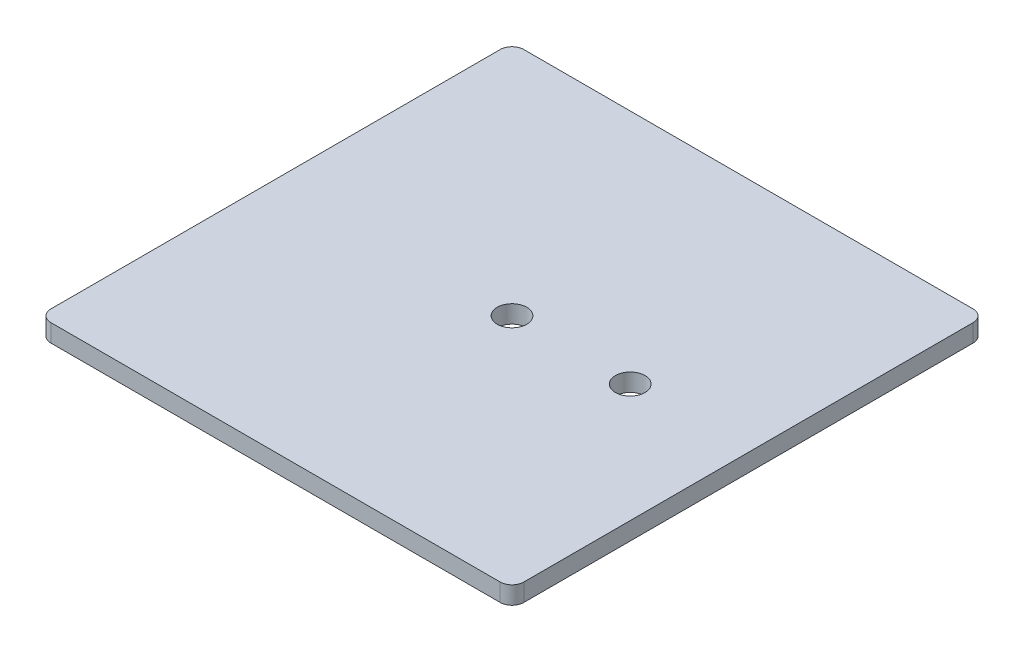
SolidWorks part; units mm, degrees
ref_plane "Face" through (0, 0, 0) normal (0, 0, 1) x (1, 0, 0)
ref_plane "Dessus" through (0, 0, 0) normal (0, 1, 0) x (1, 0, 0)
ref_plane "Droite" through (0, 0, 0) normal (1, 0, 0) x (0, 0, -1)
sketch "Esquisse1" plane through (0, 0, 0) normal (0, 1, 0) x (1, 0, 0)
  line L0 (0, 40) -> (80, 40) construction
  line L1 (0, 0) -> (80, 0)
  line L2 (0, 0) -> (0, 80)
  line L3 (0, 80) -> (80, 80)
  line L4 (80, 0) -> (80, 80)
  circle A0 centre (40, 40) radius 2.5
  circle A1 centre (60, 40) radius 2.5
  dimension "D2" = 5
  dimension "D1" = 80
  dimension "D3" = 20
extrude "Extrusion1" add sketch "Esquisse1" along normal blind 3
fillet "Congé1" radius 2 4 edges at (80, 1.5, -80) (80, 1.5, 0) (0, 1.5, -80) (0, 1.5, 0)
